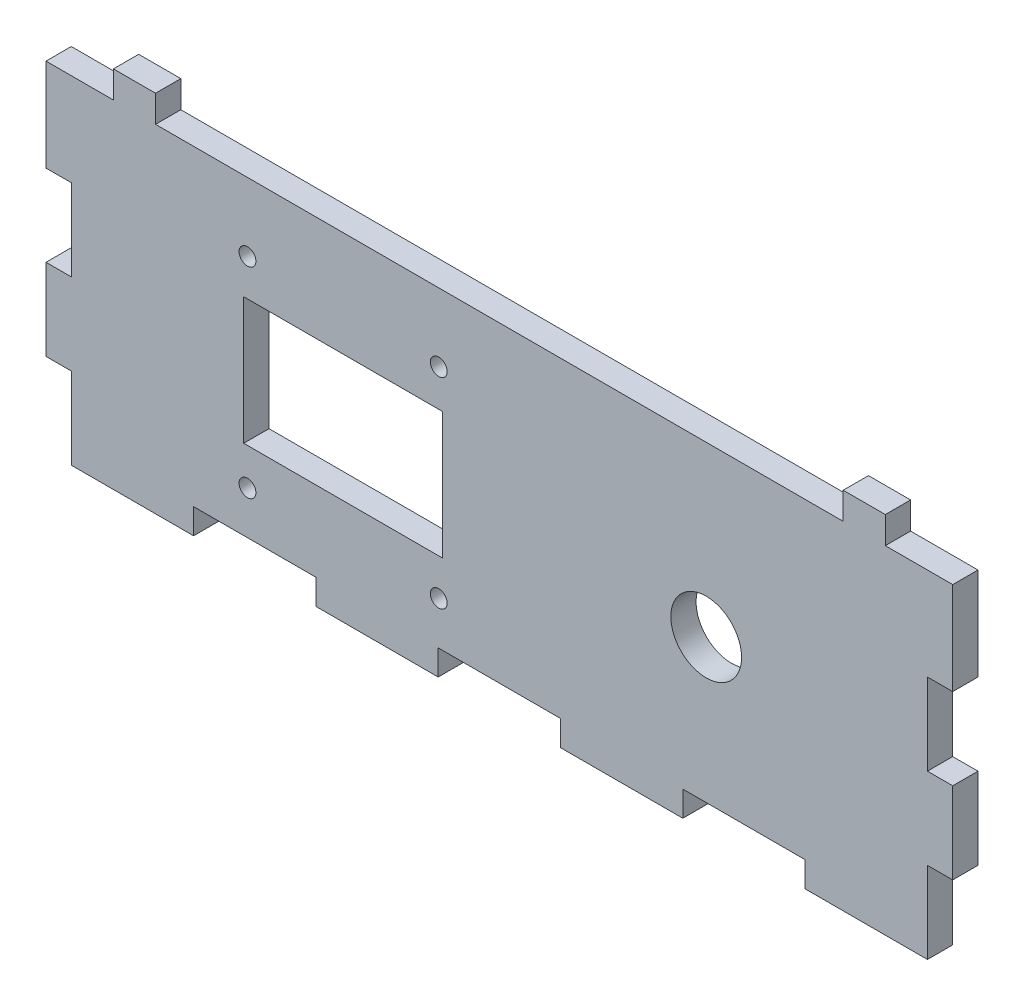
SolidWorks part; units mm, degrees
ref_plane "Alzado" through (0, 0, 0) normal (0, 0, 1) x (1, 0, 0)
ref_plane "Planta" through (0, 0, 0) normal (0, 1, 0) x (1, 0, 0)
ref_plane "Vista lateral" through (0, 0, 0) normal (1, 0, 0) x (0, 0, -1)
sketch "Croquis1" plane through (0, 0, 0) normal (0, 0, 1) x (1, 0, 0)
  line L0 (0, -17.0016) -> (0, -14.0016)
  line L1 (-48.39, -14.0016) -> (0, -14.0016) construction
  line L2 (0, -17.0016) -> (104.61, -17.0016)
  line L3 (101.61, -17.0016) -> (101.61, -49.332) construction
  line L4 (-227.956, -78.0016) -> (93.758, -78.0016) construction
  line L5 (-48.39, -14.0016) -> (-48.39, -78.0016) construction
  line L6 (78.6222, -39.0016) -> (-38.712, -39.0016) construction
  line L7 (0, -14.0016) -> (0, -17.0016) construction
  line L8 (0, -17.0016) -> (-48.39, -17.0016) construction
  line L9 (-48.39, -14.0016) -> (-38.712, -14.0016)
  line L10 (-38.712, -14.0016) -> (-38.712, -17.0016)
  line L11 (-38.712, -17.0016) -> (-29.034, -17.0016)
  line L12 (-29.034, -17.0016) -> (-29.034, -14.0016)
  line L13 (-29.034, -14.0016) -> (-19.356, -14.0016)
  line L14 (-19.356, -14.0016) -> (-19.356, -17.0016)
  line L15 (-19.356, -17.0016) -> (-9.678, -17.0016)
  line L16 (-9.678, -17.0016) -> (-9.678, -14.0016)
  line L17 (-9.678, -14.0016) -> (0, -14.0016)
  line L18 (104.61, -17.0016) -> (104.61, -78.0016) construction
  line L19 (104.61, -17.0016) -> (104.61, -29.2016)
  line L20 (104.61, -29.2016) -> (101.61, -29.2016)
  line L21 (101.61, -29.2016) -> (101.61, -41.4016)
  line L22 (101.61, -41.4016) -> (104.61, -41.4016)
  line L23 (104.61, -41.4016) -> (104.61, -53.6016)
  line L24 (104.61, -53.6016) -> (101.61, -53.6016)
  line L25 (101.61, -53.6016) -> (101.61, -65.8016)
  line L26 (101.61, -65.8016) -> (104.61, -65.8016)
  line L27 (104.61, -65.8016) -> (104.61, -78.0016)
  line L28 (-45.39, -56.5563) -> (-45.39, 45.6638) construction
  line L29 (-48.39, -14.0016) -> (-48.39, -26.8016)
  line L30 (-48.39, -26.8016) -> (-45.39, -26.8016)
  line L31 (-45.39, -26.8016) -> (-45.39, -39.6016)
  line L32 (-45.39, -39.6016) -> (-48.39, -39.6016)
  line L33 (-48.39, -39.6016) -> (-48.39, -52.4016)
  line L34 (-48.39, -52.4016) -> (-45.39, -52.4016)
  line L35 (-45.39, -52.4016) -> (-45.39, -65.2016)
  line L36 (-45.39, -65.2016) -> (-48.39, -65.2016)
  line L37 (-48.39, -65.2016) -> (-48.39, -78.0016)
  line L38 (-102.5031, -75.0016) -> (75.9308, -75.0016) construction
  line L39 (-124.386, -156.1001) -> (179.1879, -156.1001) construction
  line L40 (-48.39, -153.1001) -> (104.61, -153.1001) construction
  line L41 (-48.39, -78.0016) -> (-34.4809, -78.0016)
  line L42 (-34.4809, -78.0016) -> (-34.4809, -75.0016)
  line L43 (-34.4809, -75.0016) -> (-20.5718, -75.0016)
  line L44 (-20.5718, -75.0016) -> (-20.5718, -78.0016)
  line L45 (-20.5718, -78.0016) -> (-6.6627, -78.0016)
  line L46 (-6.6627, -78.0016) -> (-6.6627, -75.0016)
  line L47 (-6.6627, -75.0016) -> (7.2464, -75.0016)
  line L48 (7.2464, -75.0016) -> (7.2464, -78.0016)
  line L49 (7.2464, -78.0016) -> (21.1555, -78.0016)
  line L50 (21.1555, -78.0016) -> (21.1555, -75.0016)
  line L51 (21.1555, -75.0016) -> (35.0645, -75.0016)
  line L52 (35.0645, -75.0016) -> (35.0645, -78.0016)
  line L53 (35.0645, -78.0016) -> (48.9736, -78.0016)
  line L54 (48.9736, -78.0016) -> (48.9736, -75.0016)
  line L55 (48.9736, -75.0016) -> (62.8827, -75.0016)
  line L56 (62.8827, -75.0016) -> (62.8827, -78.0016)
  line L57 (62.8827, -78.0016) -> (76.7918, -78.0016)
  line L58 (76.7918, -78.0016) -> (76.7918, -75.0016)
  line L59 (76.7918, -75.0016) -> (90.7009, -75.0016)
  line L60 (90.7009, -75.0016) -> (90.7009, -78.0016)
  line L61 (90.7009, -78.0016) -> (104.61, -78.0016)
  line L62 (-48.39, -153.1001) -> (-48.39, -260.7101) construction
  line L63 (-48.39, -260.7101) -> (104.61, -260.7101) construction
  line L64 (104.61, -153.1001) -> (104.61, -260.7101) construction
  line L65 (-68.7634, -257.7101) -> (144.8732, -257.7101) construction
  line L66 (101.61, -78.0016) -> (101.61, -269.1968) construction
  line L67 (-45.39, -153.1001) -> (-45.39, -251.8965) construction
  line L68 (-34.4809, -78.0016) -> (-34.4809, -243.0877) construction
  line L69 (-20.5718, -78.0016) -> (-20.5718, -243.0877) construction
  line L70 (-6.6627, -75.0016) -> (-6.6627, -243.0877) construction
  line L71 (7.2464, -75.0016) -> (7.2464, -243.0877) construction
  line L72 (21.1555, -75.0016) -> (21.1555, -243.0877) construction
  line L73 (35.0645, -75.0016) -> (35.0645, -243.0877) construction
  line L74 (48.9736, -75.0016) -> (48.9736, -243.0877) construction
  line L75 (62.8827, -75.0016) -> (62.8827, -243.0877) construction
  line L76 (76.7918, -75.0016) -> (76.7918, -243.0877) construction
  line L77 (90.7009, -75.0016) -> (90.7009, -243.0877) construction
  line L78 (-34.4809, -156.1001) -> (-48.39, -156.1001)
  line L79 (-34.4809, -156.1001) -> (-34.4809, -153.1001)
  line L80 (-34.4809, -153.1001) -> (-20.5718, -153.1001)
  line L81 (-20.5718, -153.1001) -> (-20.5718, -156.1001)
  line L82 (-20.5718, -156.1001) -> (-6.6627, -156.1001)
  line L83 (-6.6627, -156.1001) -> (-6.6627, -153.1001)
  line L84 (-6.6627, -153.1001) -> (7.2464, -153.1001)
  line L85 (7.2464, -153.1001) -> (7.2464, -156.1001)
  line L86 (7.2464, -156.1001) -> (21.1555, -156.1001)
  line L87 (21.1555, -156.1001) -> (21.1555, -153.1001)
  line L88 (21.1555, -153.1001) -> (35.0645, -153.1001)
  line L89 (35.0645, -153.1001) -> (35.0645, -156.1001)
  line L90 (35.0645, -156.1001) -> (48.9736, -156.1001)
  line L91 (48.9736, -156.1001) -> (48.9736, -153.1001)
  line L92 (48.9736, -153.1001) -> (62.8827, -153.1001)
  line L93 (62.8827, -153.1001) -> (62.8827, -156.1001)
  line L94 (62.8827, -156.1001) -> (76.7918, -156.1001)
  line L95 (76.7918, -156.1001) -> (76.7918, -153.1001)
  line L96 (76.7918, -153.1001) -> (90.7009, -153.1001)
  line L97 (90.7009, -153.1001) -> (90.7009, -156.1001)
  line L98 (90.7009, -156.1001) -> (104.61, -156.1001)
  line L99 (-48.39, -257.7101) -> (-34.4809, -257.7101)
  line L100 (-34.4809, -257.7101) -> (-34.4809, -260.7101)
  line L101 (-34.4809, -260.7101) -> (-20.5718, -260.7101)
  line L102 (-20.5718, -260.7101) -> (-20.5718, -257.7101)
  line L103 (-20.5718, -257.7101) -> (-6.6627, -257.7101)
  line L104 (-6.6627, -257.7101) -> (-6.6627, -260.7101)
  line L105 (-6.6627, -260.7101) -> (7.2464, -260.7101)
  line L106 (7.2464, -260.7101) -> (7.2464, -257.7101)
  line L107 (7.2464, -257.7101) -> (21.1555, -257.7101)
  line L108 (21.1555, -257.7101) -> (21.1555, -260.7101)
  line L109 (21.1555, -260.7101) -> (35.0645, -260.7101)
  line L110 (35.0645, -260.7101) -> (35.0645, -257.7101)
  line L111 (35.0645, -257.7101) -> (48.9736, -257.7101)
  line L112 (48.9736, -257.7101) -> (48.9736, -260.7101)
  line L113 (48.9736, -260.7101) -> (62.8827, -260.7101)
  line L114 (62.8827, -260.7101) -> (62.8827, -257.7101)
  line L115 (62.8827, -257.7101) -> (76.7918, -257.7101)
  line L116 (76.7918, -257.7101) -> (76.7918, -260.7101)
  line L117 (76.7918, -260.7101) -> (90.7009, -260.7101)
  line L118 (90.7009, -260.7101) -> (90.7009, -257.7101)
  line L119 (90.7009, -257.7101) -> (104.61, -257.7101)
  line L120 (-226.2526, -14.0016) -> (-226.2526, -78.0016) construction
  line L121 (-290.2526, -78.0016) -> (-226.2526, -78.0016) construction
  line L122 (-226.2526, -78.0016) -> (-226.2526, -287.7111) construction
  line L123 (-290.2526, -78.0016) -> (-290.2526, -287.7111) construction
  line L124 (-290.2526, -287.7111) -> (-226.2526, -287.7111) construction
  line L125 (-48.39, -26.8016) -> (-105.5506, -26.8016) construction
  line L126 (-48.39, -39.6016) -> (-94.7516, -39.6016) construction
  line L127 (-48.39, -52.4016) -> (-71.8061, -52.4016) construction
  line L128 (-48.39, -65.2016) -> (-67.7461, -65.2016) construction
  line L129 (-277.4526, -73.8444) -> (-277.4526, -111.8004) construction
  line L130 (-264.6526, -73.8444) -> (-264.6526, -111.8004) construction
  line L131 (-251.8526, -90.832) -> (-251.8526, -128.788) construction
  line L132 (-239.0526, -73.8444) -> (-239.0526, -111.8004) construction
  line L133 (-229.2526, -73.8444) -> (-229.2526, -93.389) construction
  line L134 (165.3571, -156.1001) -> (174.5571, -156.1001)
  line L135 (174.5571, -156.1001) -> (174.5571, -153.1001)
  line L136 (174.5571, -153.1001) -> (186.7571, -153.1001)
  line L137 (186.7571, -153.1001) -> (186.7571, -156.1001)
  line L138 (186.7571, -156.1001) -> (198.9571, -156.1001)
  line L139 (198.9571, -156.1001) -> (198.9571, -153.1001)
  line L140 (198.9571, -153.1001) -> (211.1571, -153.1001)
  line L141 (211.1571, -153.1001) -> (211.1571, -156.1001)
  line L142 (211.1571, -156.1001) -> (223.3571, -156.1001)
  line L143 (-229.2526, -156.1001) -> (-229.2526, -170.6158)
  line L144 (-229.2526, -170.6158) -> (-226.2526, -170.6158)
  line L145 (-226.2526, -170.6158) -> (-226.2526, -185.1315)
  line L146 (-226.2526, -185.1315) -> (-229.2526, -185.1315)
  line L147 (-229.2526, -185.1315) -> (-229.2526, -199.6473)
  line L148 (-229.2526, -199.6473) -> (-226.2526, -199.6473)
  line L149 (-226.2526, -199.6473) -> (-226.2526, -220.163)
  line L150 (-226.2526, -220.163) -> (-229.2526, -220.163)
  line L151 (-48.39, -257.7101) -> (-48.39, -243.1944)
  line L152 (-48.39, -243.1944) -> (-45.39, -243.1944)
  line L153 (-45.39, -243.1944) -> (-45.39, -228.6787)
  line L154 (-45.39, -228.6787) -> (-48.39, -228.6787)
  line L155 (-48.39, -228.6787) -> (-48.39, -214.163)
  line L156 (-48.39, -214.163) -> (-45.39, -214.163)
  line L157 (-45.39, -214.163) -> (-45.39, -199.6473)
  line L158 (-45.39, -199.6473) -> (-48.39, -199.6473)
  line L159 (-48.39, -199.6473) -> (-48.39, -185.1315)
  line L160 (-48.39, -185.1315) -> (-45.39, -185.1315)
  line L161 (-45.39, -185.1315) -> (-45.39, -170.6158)
  line L162 (-45.39, -170.6158) -> (-48.39, -170.6158)
  line L163 (-48.39, -170.6158) -> (-48.39, -156.1001)
  line L164 (-48.39, -228.6787) -> (-80.3979, -228.6787) construction
  line L165 (-48.39, -243.1944) -> (-76.899, -243.1944) construction
  line L166 (-48.39, -214.163) -> (-74.7996, -214.163) construction
  line L167 (-48.39, -199.6473) -> (-74.7996, -199.6473) construction
  line L168 (-74.7996, -185.1315) -> (-48.39, -185.1315) construction
  line L169 (-48.39, -170.6158) -> (-71.0675, -170.6158) construction
  line L170 (-229.2526, -220.163) -> (-229.2526, -234.6787)
  line L171 (-287.2526, -73.8444) -> (-287.2526, -109.848) construction
  line L172 (-229.2526, -234.6787) -> (-226.2526, -234.6787)
  line L173 (-226.2526, -234.6787) -> (-226.2526, -249.1944)
  line L174 (-226.2526, -249.1944) -> (-229.2526, -249.1944)
  line L175 (-229.2526, -249.1944) -> (-229.2526, -257.7101)
  line L176 (223.3571, -257.7101) -> (211.1571, -257.7101)
  line L177 (211.1571, -257.7101) -> (211.1571, -260.7101)
  line L178 (211.1571, -260.7101) -> (198.9571, -260.7101)
  line L179 (198.9571, -260.7101) -> (198.9571, -257.7101)
  line L180 (198.9571, -257.7101) -> (186.7571, -257.7101)
  line L181 (186.7571, -257.7101) -> (186.7571, -260.7101)
  line L182 (186.7571, -260.7101) -> (174.5571, -260.7101)
  line L183 (174.5571, -260.7101) -> (174.5571, -257.7101)
  line L184 (-287.2526, -257.7101) -> (-287.2526, -243.1944)
  line L185 (-287.2526, -243.1944) -> (-290.2526, -243.1944)
  line L186 (-290.2526, -243.1944) -> (-290.2526, -228.6787)
  line L187 (-290.2526, -228.6787) -> (-287.2526, -228.6787)
  line L188 (-287.2526, -228.6787) -> (-287.2526, -214.163)
  line L189 (-287.2526, -214.163) -> (-290.2526, -214.163)
  line L190 (-290.2526, -214.163) -> (-290.2526, -199.6473)
  line L191 (-290.2526, -199.6473) -> (-287.2526, -199.6473)
  line L192 (-287.2526, -199.6473) -> (-287.2526, -185.1315)
  line L193 (-287.2526, -185.1315) -> (-290.2526, -185.1315)
  line L194 (-290.2526, -185.1315) -> (-290.2526, -170.6158)
  line L195 (-290.2526, -170.6158) -> (-287.2526, -170.6158)
  line L196 (-287.2526, -170.6158) -> (-287.2526, -156.1001)
  line L197 (174.5571, -257.7101) -> (165.3571, -257.7101)
  line L198 (-315.487, -120.5373) -> (-315.487, -274.6014) construction
  line L199 (-423.097, -153.1001) -> (-423.097, -80.2802) construction
  line L200 (-420.097, -153.1001) -> (-420.097, -73.0846) construction
  line L201 (-405.5813, -153.1001) -> (-405.5813, -73.0846) construction
  line L202 (-391.0655, -153.1001) -> (-391.0655, -77.6291) construction
  line L203 (-376.5498, -153.1001) -> (-376.5498, -80.2802) construction
  line L204 (-362.0341, -153.1001) -> (-362.0341, -73.0846) construction
  line L205 (-347.5184, -153.1001) -> (-347.5184, -77.6291) construction
  line L206 (-333.0027, -153.1001) -> (-333.0027, -73.0846) construction
  line L207 (-318.487, -153.1001) -> (-318.487, -77.6291) construction
  line L208 (-48.39, -21.6772) -> (-48.39, 38.9813) construction
  line L209 (-38.712, -14.0016) -> (-38.712, 45.6638) construction
  line L210 (-29.034, -14.0016) -> (-29.034, 45.6638) construction
  line L211 (-19.356, -14.0016) -> (-19.356, 45.6638) construction
  line L212 (-9.678, -14.0016) -> (-9.678, 45.6638) construction
  line L213 (0, -14.0016) -> (0, 45.6638) construction
  line L214 (2.5149, 38.1832) -> (-48.39, 38.1832) construction
  line L215 (-48.39, 86.5732) -> (-80.1148, 86.5732) construction
  line L216 (-48.39, 76.8952) -> (-75.2531, 76.8952) construction
  line L217 (-48.39, 67.2172) -> (-75.2531, 67.2172) construction
  line L218 (-48.39, 57.5392) -> (-80.1148, 57.5392) construction
  line L219 (-48.39, 47.8612) -> (-84.9766, 47.8612) construction
  line L220 (-318.487, 38.1832) -> (-318.487, 47.8612)
  line L221 (-48.39, 38.1832) -> (-76.9441, 38.1832) construction
  line L222 (-318.487, 47.8612) -> (-315.487, 47.8612)
  line L223 (-315.487, 47.8612) -> (-315.487, 57.5392)
  line L224 (-315.487, 57.5392) -> (-318.487, 57.5392)
  line L225 (-318.487, 57.5392) -> (-318.487, 67.2172)
  line L226 (-420.097, 78.2172) -> (-415.097, 78.2172)
  line L227 (-415.097, 78.2172) -> (-415.097, 81.4172)
  line L228 (-415.097, 81.4172) -> (-410.097, 81.4172)
  line L229 (-318.487, 67.2172) -> (-315.487, 67.2172)
  line L230 (-315.487, 67.2172) -> (-315.487, 78.2172)
  line L231 (-315.487, 78.2172) -> (-318.487, 78.2172)
  line L232 (-420.097, 67.2172) -> (-423.097, 67.2172)
  line L233 (-423.097, 67.2172) -> (-423.097, 78.2172)
  line L234 (-423.097, 78.2172) -> (-420.097, 78.2172)
  line L235 (-420.097, 67.2172) -> (-420.097, 57.5392)
  line L236 (-420.097, 57.5392) -> (-423.097, 57.5392)
  line L237 (-423.097, 57.5392) -> (-423.097, 47.8612)
  line L238 (-423.097, 47.8612) -> (-420.097, 47.8612)
  line L239 (-420.097, 47.8612) -> (-420.097, 38.1832)
  line L240 (-48.39, 41.1832) -> (-83.9517, 41.1832) construction
  line L241 (-318.487, 38.1832) -> (-333.0027, 38.1832)
  line L242 (-333.0027, 38.1832) -> (-333.0027, 41.1832)
  line L243 (-333.0027, 41.1832) -> (-347.5184, 41.1832)
  line L244 (-347.5184, 41.1832) -> (-347.5184, 38.1832)
  line L245 (-347.5184, 38.1832) -> (-362.0341, 38.1832)
  line L246 (-362.0341, 38.1832) -> (-362.0341, 41.1832)
  line L247 (-362.0341, 41.1832) -> (-376.5498, 41.1832)
  line L248 (-376.5498, 41.1832) -> (-376.5498, 38.1832)
  line L249 (-376.5498, 38.1832) -> (-391.0655, 38.1832)
  line L250 (-391.0655, 38.1832) -> (-391.0655, 41.1832)
  line L251 (-391.0655, 41.1832) -> (-405.5813, 41.1832)
  line L252 (-405.5813, 41.1832) -> (-405.5813, 38.1832)
  line L253 (-405.5813, 38.1832) -> (-420.097, 38.1832)
  line L254 (162.3571, -15.1529) -> (162.3571, -104.9762) construction
  line L255 (104.61, -29.2016) -> (145.8916, -29.2016) construction
  line L256 (104.61, -41.4016) -> (145.8916, -41.4016) construction
  line L257 (104.61, -65.8016) -> (131.4417, -65.8016) construction
  line L258 (104.61, -53.6016) -> (126.5441, -53.6016) construction
  line L259 (165.3571, -73.8444) -> (165.3571, -106.8492) construction
  line L260 (174.5571, -73.8444) -> (174.5571, -108.8044) construction
  line L261 (186.7571, -73.8444) -> (186.7571, -108.8044) construction
  line L262 (198.9571, -73.8444) -> (198.9571, -108.8044) construction
  line L263 (211.1571, -73.8444) -> (211.1571, -106.8492) construction
  line L264 (223.3571, -73.8444) -> (223.3571, -108.8044) construction
  line L265 (104.61, -257.7101) -> (104.61, -243.0877)
  line L266 (104.61, -243.0877) -> (101.61, -243.0877)
  line L267 (101.61, -243.0877) -> (101.61, -228.6787)
  line L268 (101.61, -228.6787) -> (104.61, -228.6787)
  line L269 (104.61, -228.6787) -> (104.61, -214.163)
  line L270 (104.61, -214.163) -> (101.61, -214.163)
  line L271 (101.61, -214.163) -> (101.61, -199.6473)
  line L272 (101.61, -199.6473) -> (104.61, -199.6473)
  line L273 (104.61, -199.6473) -> (104.61, -185.1315)
  line L274 (104.61, -185.1315) -> (101.61, -185.1315)
  line L275 (101.61, -185.1315) -> (101.61, -170.6158)
  line L276 (101.61, -170.6158) -> (104.61, -170.6158)
  line L277 (104.61, -170.6158) -> (104.61, -156.1001)
  line L278 (-229.2526, -156.1001) -> (-239.0526, -156.1001)
  line L279 (-239.0526, -156.1001) -> (-239.0526, -153.1001)
  line L280 (-239.0526, -153.1001) -> (-251.8526, -153.1001)
  line L281 (-251.8526, -153.1001) -> (-251.8526, -156.1001)
  line L282 (-251.8526, -156.1001) -> (-264.6526, -156.1001)
  line L283 (-264.6526, -156.1001) -> (-264.6526, -153.1001)
  line L284 (-264.6526, -153.1001) -> (-277.4526, -153.1001)
  line L285 (-277.4526, -153.1001) -> (-277.4526, -156.1001)
  line L286 (-277.4526, -156.1001) -> (-287.2526, -156.1001)
  line L287 (223.3571, -156.1001) -> (223.3571, -257.7101)
  line L288 (-229.2526, -257.7101) -> (-239.0526, -257.7101)
  line L289 (-239.0526, -257.7101) -> (-239.0526, -260.7101)
  line L290 (-239.0526, -260.7101) -> (-251.8526, -260.7101)
  line L291 (-251.8526, -260.7101) -> (-251.8526, -257.7101)
  line L292 (-251.8526, -257.7101) -> (-264.6526, -257.7101)
  line L293 (-264.6526, -257.7101) -> (-264.6526, -260.7101)
  line L294 (-264.6526, -260.7101) -> (-277.4526, -260.7101)
  line L295 (-277.4526, -260.7101) -> (-277.4526, -257.7101)
  line L296 (-277.4526, -257.7101) -> (-287.2526, -257.7101)
  line L297 (165.3571, -257.7101) -> (165.3571, -243.1944)
  line L298 (165.3571, -243.1944) -> (162.3571, -243.1944)
  line L299 (162.3571, -243.1944) -> (162.3571, -228.6787)
  line L300 (162.3571, -228.6787) -> (165.3571, -228.6787)
  line L301 (165.3571, -228.6787) -> (165.3571, -214.163)
  line L302 (165.3571, -214.163) -> (162.3571, -214.163)
  line L303 (162.3571, -214.163) -> (162.3571, -199.6473)
  line L304 (162.3571, -199.6473) -> (165.3571, -199.6473)
  line L305 (165.3571, -199.6473) -> (165.3571, -185.1315)
  line L306 (165.3571, -185.1315) -> (162.3571, -185.1315)
  line L307 (162.3571, -185.1315) -> (162.3571, -170.6158)
  line L308 (162.3571, -170.6158) -> (165.3571, -170.6158)
  line L309 (165.3571, -170.6158) -> (165.3571, -156.1001)
  line L310 (-410.097, 81.4172) -> (-410.097, 78.2172)
  line L311 (-410.097, 78.2172) -> (-328.487, 78.2172)
  line L312 (-328.487, 78.2172) -> (-328.487, 81.4172)
  line L313 (-328.487, 81.4172) -> (-323.487, 81.4172)
  line L314 (-323.487, 81.4172) -> (-323.487, 78.2172)
  line L315 (-323.487, 78.2172) -> (-318.487, 78.2172)
  line L316 (-387.8334, 72.1002) -> (-387.8334, 44.3002) construction
  line L317 (-401.1834, 72.1002) -> (-374.4834, 72.1002) construction
  line L318 (-401.1834, 72.1002) -> (-401.1834, 44.3002) construction
  line L319 (-401.1834, 44.3002) -> (-374.4834, 44.3002) construction
  line L320 (-374.4834, 72.1002) -> (-374.4834, 44.3002) construction
  line L321 (-410.097, 78.2172) -> (-410.097, 38.1832) construction
  line L322 (-410.097, 58.2002) -> (-333.0027, 58.2002) construction
  line L324 (-401.1834, 67.8302) -> (-374.4834, 67.8302) construction
  line L325 (-401.1834, 67.8302) -> (-401.1834, 48.5702) construction
  line L326 (-401.1834, 48.5702) -> (-374.4834, 48.5702) construction
  line L327 (-374.4834, 67.8302) -> (-374.4834, 48.5702) construction
  line L328 (-399.632, 65.7302) -> (-376.0348, 65.7302)
  line L329 (-399.632, 65.7302) -> (-399.632, 50.6702)
  line L330 (-399.632, 50.6702) -> (-376.0348, 50.6702)
  line L331 (-376.0348, 65.7302) -> (-376.0348, 50.6702)
  circle A0 centre (73.11, -39.0016) radius 1.25
  circle A1 centre (31.5, -39.0016) radius 1.25
  circle A2 centre (-28.49, -39.0016) radius 1.25
  arc A3 (-226.2526, -65.2016) -> (-239.0526, -78.0016) centre (-226.2526, -78.0016) ccw construction
  arc A4 (-226.2526, -52.4016) -> (-251.8526, -78.0016) centre (-226.2526, -78.0016) ccw construction
  arc A5 (-226.2526, -39.6016) -> (-264.6526, -78.0016) centre (-226.2526, -78.0016) ccw construction
  arc A6 (-226.2526, -26.8016) -> (-277.4526, -78.0016) centre (-226.2526, -78.0016) ccw construction
  arc A7 (-226.2526, -14.0016) -> (-290.2526, -78.0016) centre (-226.2526, -78.0016) ccw construction
  arc A8 (-226.2526, -75.0016) -> (-229.2526, -78.0016) centre (-226.2526, -78.0016) ccw construction
  arc A9 (-226.2526, -17.0016) -> (-287.2526, -78.0016) centre (-226.2526, -78.0016) ccw construction
  arc A10 (-315.487, -156.1001) -> (-318.487, -153.1001) centre (-315.487, -153.1001) cw construction
  arc A11 (-315.487, -170.6158) -> (-333.0027, -153.1001) centre (-315.487, -153.1001) cw construction
  arc A12 (-315.487, -185.1315) -> (-347.5184, -153.1001) centre (-315.487, -153.1001) cw construction
  arc A13 (-315.487, -199.6473) -> (-362.0341, -153.1001) centre (-315.487, -153.1001) cw construction
  arc A14 (-315.487, -214.163) -> (-376.5498, -153.1001) centre (-315.487, -153.1001) cw construction
  arc A15 (-315.487, -228.6787) -> (-391.0655, -153.1001) centre (-315.487, -153.1001) cw construction
  arc A16 (-315.487, -243.1944) -> (-405.5813, -153.1001) centre (-315.487, -153.1001) cw construction
  arc A17 (-315.487, -257.7101) -> (-420.097, -153.1001) centre (-315.487, -153.1001) cw construction
  arc A18 (-315.487, -260.7101) -> (-423.097, -153.1001) centre (-315.487, -153.1001) cw construction
  arc A19 (-45.39, 38.1832) -> (-48.39, 41.1832) centre (-48.39, 38.1832) ccw construction
  arc A20 (-38.712, 38.1832) -> (-48.39, 47.8612) centre (-48.39, 38.1832) ccw construction
  arc A21 (-29.034, 38.1832) -> (-48.39, 57.5392) centre (-48.39, 38.1832) ccw construction
  arc A22 (-19.356, 38.1832) -> (-48.39, 67.2172) centre (-48.39, 38.1832) ccw construction
  arc A23 (-9.678, 38.1832) -> (-48.39, 76.8952) centre (-48.39, 38.1832) ccw construction
  arc A24 (0, 38.1832) -> (-48.39, 86.5732) centre (-48.39, 38.1832) ccw construction
  arc A25 (162.3571, -75.0016) -> (165.3571, -78.0016) centre (162.3571, -78.0016) cw construction
  arc A26 (162.3571, -65.8016) -> (174.5571, -78.0016) centre (162.3571, -78.0016) cw construction
  arc A27 (162.3571, -53.6016) -> (186.7571, -78.0016) centre (162.3571, -78.0016) cw construction
  arc A28 (162.3571, -41.4016) -> (198.9571, -78.0016) centre (162.3571, -78.0016) cw construction
  arc A29 (162.3571, -29.2016) -> (211.1571, -78.0016) centre (162.3571, -78.0016) cw construction
  arc A30 (162.3571, -17.0016) -> (223.3571, -78.0016) centre (162.3571, -78.0016) cw construction
  circle A31 centre (-376.4834, 70.1002) radius 1
  circle A32 centre (-376.4834, 46.3002) radius 1
  circle A33 centre (-399.1834, 46.3002) radius 1
  circle A34 centre (-399.1834, 70.1002) radius 1
  circle A35 centre (-344.744, 58.2002) radius 4.2
  text T0 "TOP\r\n"
  point P465 (-387.8334, 58.2002)
  dimension "D2" = 2.5
  dimension "D3" = 2.5
  dimension "D4" = 2.5
  dimension "D7" = 101.6
  dimension "D20" = 22
  dimension "D9" = 36
  dimension "D26" = 19.26
  dimension "D24" = 4.27
  dimension "D28" = 2
  dimension "D33" = 8.4
  dimension "D1" = 153
  dimension "D5" = 3
  dimension "D6" = 104.61
  dimension "D8" = 3
  dimension "D10" = 3
  dimension "D11" = 41.61
  dimension "D12" = 5
  dimension "D13" = 3
  dimension "D14" = 153
  dimension "D15" = 107.61
  dimension "D16" = 5
  dimension "D17" = 3
  dimension "D18" = 3
  dimension "D19" = 28.5
  dimension "D21" = 5
  dimension "D22" = 5
  dimension "D23" = 3.2
  dimension "D25" = 26.7
  dimension "D27" = 2.1
  dimension "D32" = 27.8
extrude "Saliente-Extruir1" add sketch "Croquis1" along normal blind 3
